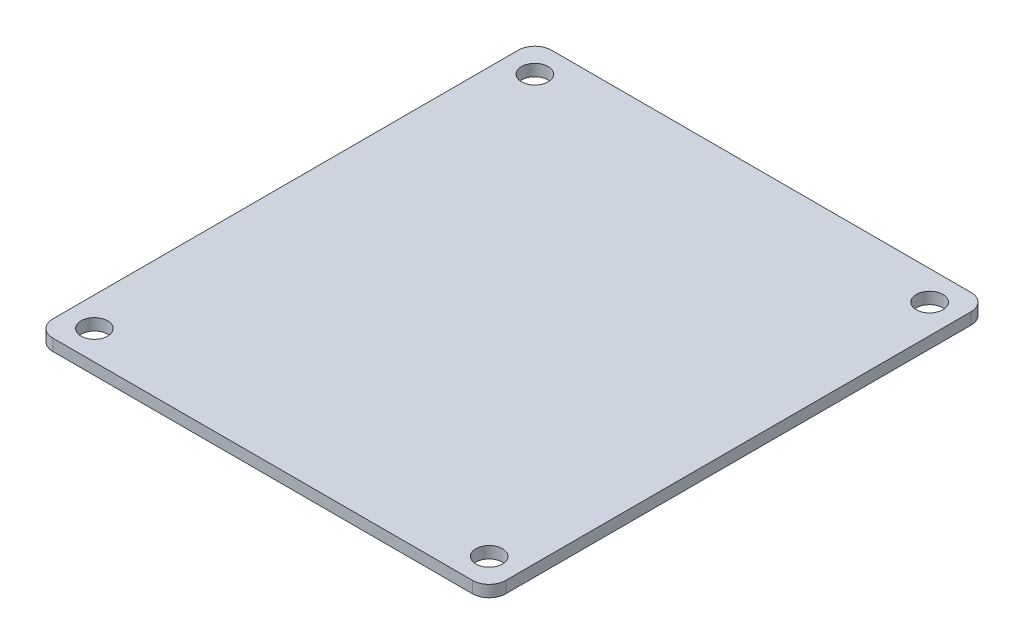
SolidWorks part; units mm, degrees
ref_plane "Front Plane" through (0, 0, 0) normal (0, 0, 1) x (1, 0, 0)
ref_plane "Top Plane" through (0, 0, 0) normal (0, 1, 0) x (1, 0, 0)
ref_plane "Right Plane" through (0, 0, 0) normal (1, 0, 0) x (0, 0, -1)
sketch "Sketch1" plane through (0, 0, 0) normal (0, 1, 0) x (1, 0, 0)
  line L1 (27.25, -30) -> (-27.25, -30)
  line L2 (27.25, -30) -> (27.25, 30)
  line L3 (27.25, 30) -> (-27.25, 30)
  line L4 (-27.25, -30) -> (-27.25, 30)
  line L5 (27.25, -30) -> (-27.25, 30) construction
  line L6 (27.25, 30) -> (-27.25, -30) construction
  point P0 (0, 0)
extrude "Boss-Extrude1" add sketch "Sketch1" along normal blind 1.4
sketch "Sketch2" plane through (0, 1.4, 0) normal (0, 1, 0) x (1, 0, 0)
  circle A0 centre (-23.75, 26.5) radius 1.6
  circle A1 centre (-23.75, -26.5) radius 1.6
  circle A2 centre (23.75, -26.5) radius 1.6
  circle A3 centre (23.75, 26.5) radius 1.6
extrude "Cut-Extrude1" cut sketch "Sketch2" against normal through all
sketch "Sketch3" plane through (0, 1.4, 0) normal (0, 1, 0) x (1, 0, 0)
  line L0 (0, 30) -> (0, -30) construction
  line L1 (27.25, 30) -> (-27.25, 30) construction
  line L2 (-27.25, -30) -> (27.25, -30) construction
  line L3 (27.25, 0) -> (-27.25, 0) construction
  line L4 (27.25, -30) -> (27.25, 30) construction
  line L5 (-27.25, 30) -> (-27.25, -30) construction
  line L6 (28.25, 30) -> (28.25, -30) construction
  line L7 (28.25, 24) -> (28.25, 8) construction
  line L8 (-15.75, 30) -> (17.25, 30) construction
  line L9 (-15.75, 30) -> (-15.75, 27.46) construction
  line L10 (-15.75, 27.46) -> (17.25, 27.46) construction
  line L11 (17.25, 30) -> (17.25, 27.46) construction
  line L12 (-17.25, -30) -> (15.75, -30) construction
  line L13 (-17.25, -30) -> (-17.25, -25) construction
  line L14 (-17.25, -25) -> (15.75, -25) construction
  line L15 (15.75, -30) -> (15.75, -25) construction
  line L16 (28.25, 24) -> (7.25, 24) construction
  line L20 (28.25, 8) -> (7.25, 8) construction
  line L21 (31.9503, 30) -> (31.9503, 6) construction
  line L22 (7.25, 8) -> (7.25, 24) construction
  line L23 (36.4039, 30) -> (36.4039, -7) construction
  line L24 (28.25, 6) -> (20.25, 6) construction
  line L25 (28.25, 6) -> (28.25, -2) construction
  line L26 (28.25, -2) -> (20.25, -2) construction
  line L27 (20.25, 6) -> (20.25, -2) construction
  line L28 (40.3281, 30) -> (40.3281, -16.5) construction
  line L29 (28.25, -7) -> (20.75, -7) construction
  line L30 (28.25, -7) -> (28.25, -13) construction
  line L31 (28.25, -13) -> (20.75, -13) construction
  line L32 (20.75, -7) -> (20.75, -13) construction
  line L34 (28.25, -16.5) -> (14.25, -16.5) construction
  line L35 (28.25, -16.5) -> (28.25, -22.5) construction
  line L36 (28.25, -22.5) -> (14.25, -22.5) construction
  line L37 (14.25, -16.5) -> (14.25, -22.5) construction
fillet "Fillet1" radius 2 4 edges at (27.25, 0.7, -30) (-27.25, 0.7, -30) (27.25, 0.7, 30) (-27.25, 0.7, 30)
